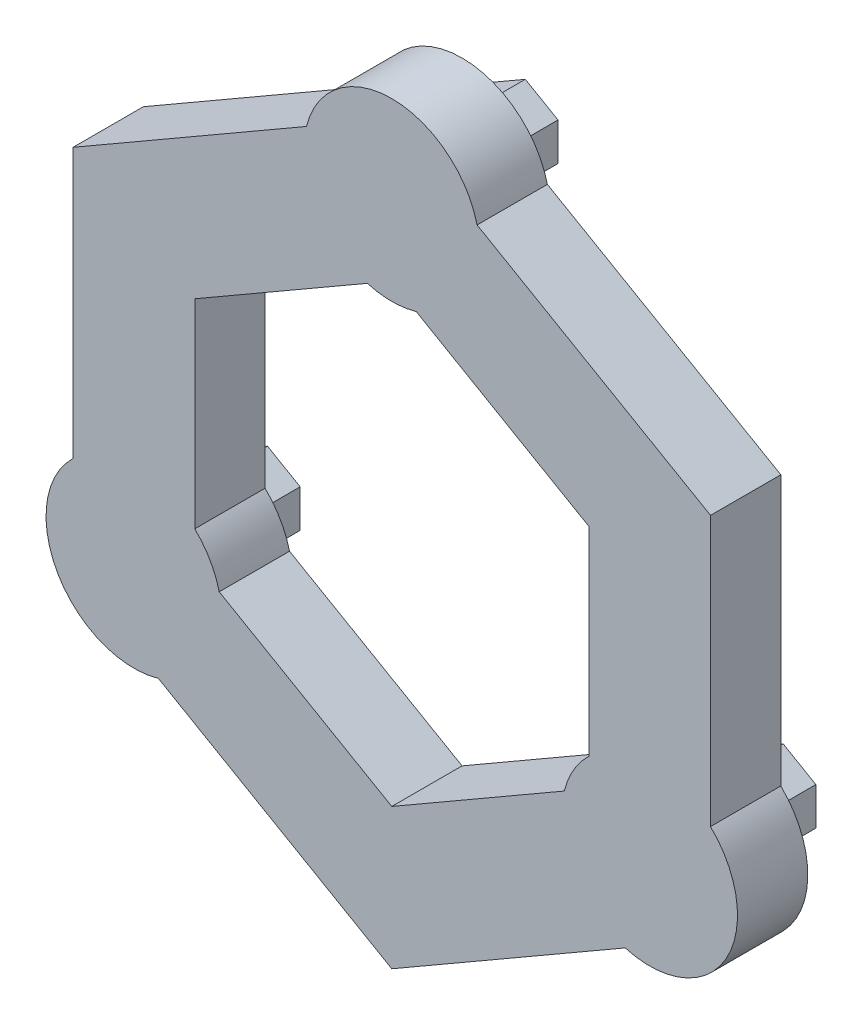
SolidWorks part; units mm, degrees
ref_plane "Front Plane" through (0, 0, 0) normal (0, 0, 1) x (1, 0, 0)
ref_plane "Top Plane" through (0, 0, 0) normal (0, 1, 0) x (1, 0, 0)
ref_plane "Right Plane" through (0, 0, 0) normal (1, 0, 0) x (0, 0, -1)
sketch "Sketch1" plane through (0, 0, 0) normal (0, 0, 1) x (1, 0, 0)
  line L0 (0, 21.1785) -> (0, 0) construction
  line L1 (0, 0) -> (18.3411, -10.5892) construction
  line L2 (0, 0) -> (-18.3411, -10.5892) construction
  line L3 (0, 21.1785) -> (0, 42.357) construction
  line L4 (0, -10.45) -> (0, 10.45) construction
  line L5 (18.3411, -10.5892) -> (36.6822, -21.1785) construction
  line L6 (-18.3411, -10.5892) -> (-36.6822, -21.1785) construction
  circle A0 centre (0, 0) radius 21.1785 construction
  circle A1 centre (0, 42.357) radius 21.1785 construction
  circle A2 centre (36.6822, -21.1785) radius 21.1785 construction
  circle A3 centre (-36.6822, -21.1785) radius 21.1785 construction
  dimension "D3" = 42.357
  dimension "D4" = 42.357
  dimension "D1" = 120
  dimension "D2" = 120
sketch "Sketch3" plane through (0, 0, 0) normal (0, 0, 1) x (1, 0, 0)
  line L0 (0, -10.45) -> (0, 10.45) construction
  line L1 (0, 42.357) -> (-36.6822, 21.1785) construction
  line L2 (-36.6822, 21.1785) -> (-36.6822, -21.1785) construction
  line L3 (-36.6822, -21.1785) -> (0, -42.357) construction
  line L4 (0, -42.357) -> (36.6822, -21.1785) construction
  line L5 (36.6822, -21.1785) -> (36.6822, 21.1785) construction
  line L6 (36.6822, 21.1785) -> (0, 42.357) construction
  line L7 (0, 32.357) -> (-28.022, 16.1785)
  line L8 (-28.022, 16.1785) -> (-28.022, -16.1785)
  line L9 (-28.022, -16.1785) -> (0, -32.357)
  line L10 (0, -32.357) -> (28.022, -16.1785)
  line L11 (28.022, -16.1785) -> (28.022, 16.1785)
  line L12 (28.022, 16.1785) -> (0, 32.357)
  line L13 (0, 52.357) -> (-45.3425, 26.1785)
  line L14 (-45.3425, 26.1785) -> (-45.3425, -26.1785)
  line L15 (-45.3425, -26.1785) -> (0, -52.357)
  line L16 (0, -52.357) -> (45.3425, -26.1785)
  line L17 (45.3425, -26.1785) -> (45.3425, 26.1785)
  line L18 (45.3425, 26.1785) -> (0, 52.357)
  line L19 (0, 21.1785) -> (0, 42.357) construction
  line L20 (-45.3425, 26.1785) -> (-28.022, 16.1785) construction
  circle A0 centre (0, 0) radius 36.6822 construction
  circle A1 centre (0, 0) radius 28.022 construction
  circle A2 centre (0, 0) radius 45.3425 construction
  circle A3 centre (-36.6822, -21.1785) radius 12.5
  circle A4 centre (36.6822, -21.1785) radius 12.5
  circle A5 centre (0, 42.357) radius 12.5
  point P35 (-36.6822, 21.1785)
  dimension "D2" = 25
  dimension "D1" = 20
extrude "Boss-Extrude2" add sketch "Sketch3" along normal mid plane 10 contours A5 L7 L8 A3 L9 L10 A4 L11 L12 | L14 A3 L15 | L16 A4 L17 | L18 A5 L13
sketch "Sketch4" plane through (0, 0, -5) normal (0, 0, -1) x (-1, 0, 0)
  line L1 (-41.3322, -23.8632) -> (-36.6822, -26.5479)
  line L2 (-36.6822, -26.5479) -> (-32.0322, -23.8632)
  line L3 (-32.0322, -23.8632) -> (-32.0322, -18.4938)
  line L4 (-32.0322, -18.4938) -> (-36.6822, -15.8091)
  line L5 (-36.6822, -15.8091) -> (-41.3322, -18.4938)
  line L6 (-41.3322, -18.4938) -> (-41.3322, -23.8632)
  line L7 (41.3322, -23.8632) -> (41.3322, -18.4938)
  line L8 (41.3322, -18.4938) -> (36.6822, -15.8091)
  line L9 (36.6822, -15.8091) -> (32.0322, -18.4938)
  line L10 (32.0322, -18.4938) -> (32.0322, -23.8632)
  line L11 (32.0322, -23.8632) -> (36.6822, -26.5479)
  line L12 (36.6822, -26.5479) -> (41.3322, -23.8632)
  line L13 (0, 47.7264) -> (-4.65, 45.0417)
  line L14 (-4.65, 45.0417) -> (-4.65, 39.6723)
  line L15 (-4.65, 39.6723) -> (0, 36.9876)
  line L16 (0, 36.9876) -> (4.65, 39.6723)
  line L17 (4.65, 39.6723) -> (4.65, 45.0417)
  line L18 (4.65, 45.0417) -> (0, 47.7264)
  circle A0 centre (-36.6822, -21.1785) radius 4.65 construction
  circle A1 centre (36.6822, -21.1785) radius 4.65 construction
  circle A2 centre (0, 42.357) radius 4.65 construction
  dimension "D1" = 9.3
extrude "Boss-Extrude3" add sketch "Sketch4" along normal blind 9
equation "\"sN\"= 12'Sun teeth"
equation "\"rN\"= 36'Ring teeth"
equation "\"pN\"= ( \"rN\" - \"sN\" ) / 2'Planet teeth"
equation "\"m\"= 3.5'Modulus"
equation "\"sRD\"= \"sN\" * \"m\"'Sun root diam"
equation "\"rRD\"= \"rN\" * \"m\"'Ring root diam"
equation "\"pRD\"= \"pN\" * \"m\"'Planet root diam"
equation "\"D3@Sketch1\"=\"sRD\"*\"sF\""
equation "\"D4@Sketch1\"=\"pRD\"*\"sF\""
equation "\"sF\"= 1.0085'Scale factor"
